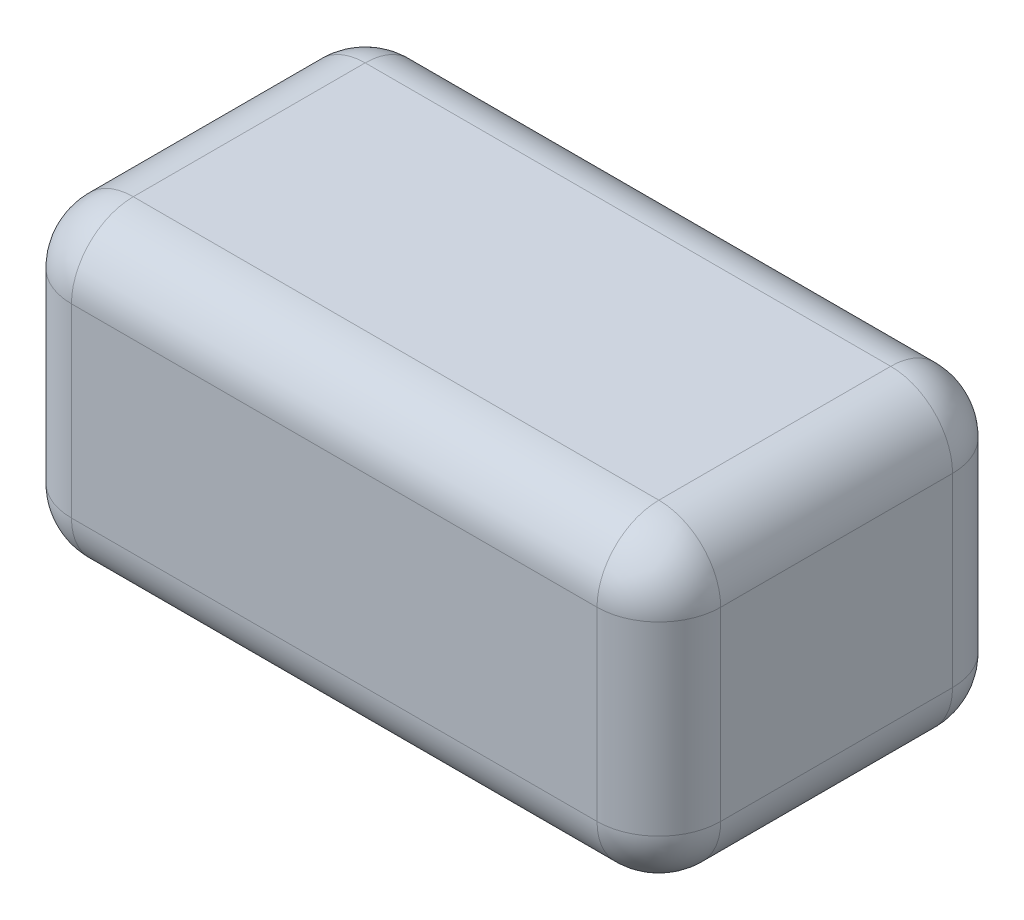
SolidWorks part; units mm, degrees
ref_plane "Front Plane" through (0, 0, 0) normal (0, 0, 1) x (1, 0, 0)
ref_plane "Top Plane" through (0, 0, 0) normal (0, 1, 0) x (1, 0, 0)
ref_plane "Right Plane" through (0, 0, 0) normal (1, 0, 0) x (0, 0, -1)
sketch "Sketch1" plane through (0, 0, 0) normal (0, 1, 0) x (1, 0, 0)
  line L1 (-40.1154, 3.1973) -> (1.8846, 3.1973)
  line L2 (-40.1154, 3.1973) -> (-40.1154, -19.8027)
  line L3 (-40.1154, -19.8027) -> (1.8846, -19.8027)
  line L4 (1.8846, 3.1973) -> (1.8846, -19.8027)
  dimension "D1" = 42
  dimension "D2" = 23
extrude "Boss-Extrude1" add sketch "Sketch1" along normal blind 20
fillet "Fillet1" radius 4 12 edges at (-40.1154, 10, 19.8027) (1.8846, 10, 19.8027) (1.8846, 10, -3.1973) (-40.1154, 10, -3.1973) (-19.1154, 20, -3.1973) (1.8846, 20, 8.3027) (-19.1154, 20, 19.8027) (-40.1154, 20, 8.3027) (-19.1154, 0, -3.1973) (1.8846, 0, 8.3027) (-19.1154, 0, 19.8027) (-40.1154, 0, 8.3027)
